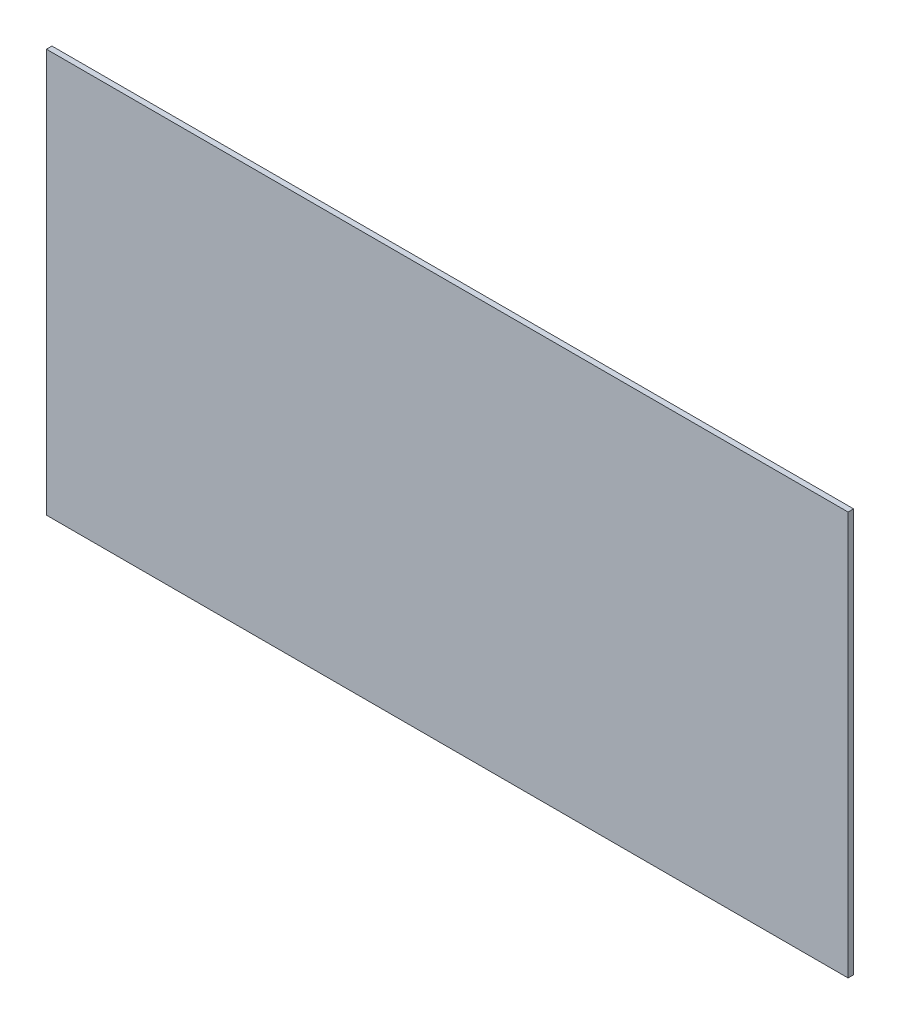
SolidWorks part; units mm, degrees
ref_plane "Front Plane" through (0, 0, 0) normal (0, 0, 1) x (1, 0, 0)
ref_plane "Top Plane" through (0, 0, 0) normal (0, 1, 0) x (1, 0, 0)
ref_plane "Right Plane" through (0, 0, 0) normal (1, 0, 0) x (0, 0, -1)
sketch "Sketch1" plane through (0, 0, 0) normal (0, 0, 1) x (1, 0, 0)
  line L1 (0, 0) -> (-291.2, 0)
  line L2 (0, 0) -> (0, 146.59)
  line L3 (0, 146.59) -> (-291.2, 146.59)
  line L4 (-291.2, 0) -> (-291.2, 146.59)
  dimension "D1" = 146.59
  dimension "D2" = 291.2
extrude "Boss-Extrude1" add sketch "Sketch1" along normal blind 2
